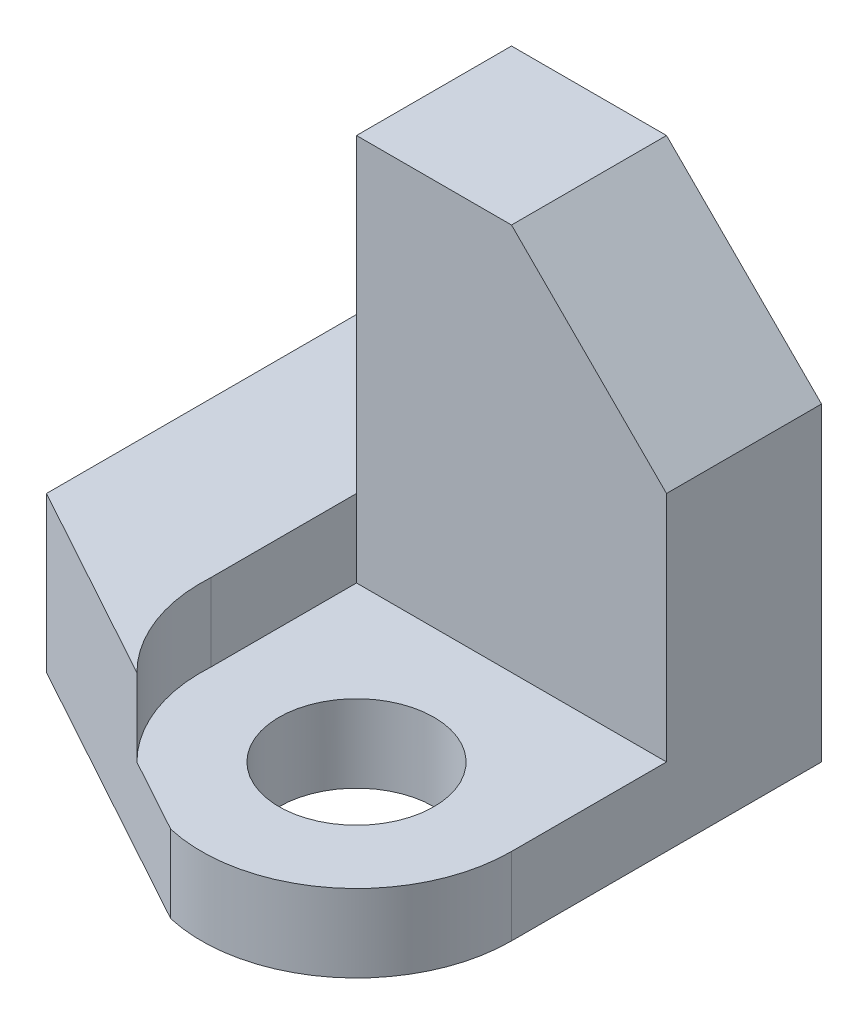
SolidWorks part; units mm, degrees
ref_plane "Front" through (0, 0, 0) normal (0, 0, 1) x (1, 0, 0)
ref_plane "Top" through (0, 0, 0) normal (0, 1, 0) x (1, 0, 0)
ref_plane "Right" through (0, 0, 0) normal (1, 0, 0) x (0, 0, -1)
sketch "Sketch1" plane through (0, 0, 0) normal (0, 1, 0) x (1, 0, 0)
  line L0 (0, 0) -> (4, 0)
  line L1 (4, 0) -> (4, -4)
  line L2 (0, -4) -> (0, 0)
  line L3 (0, 0) -> (-2, 0)
  line L4 (-2, 0) -> (-2, -4)
  line L5 (-2, -4) -> (1.5528, -5.9494)
  arc A0 (4, -4) -> (0, -4) centre (2, -4) cw
  circle A1 centre (2, -4) radius 1
  dimension "D5" = 2
  dimension "D1" = 4
  dimension "D2" = 4
  dimension "D3" = 2
  dimension "D4" = 4
extrude "Boss-Extrude1" add sketch "Sketch1" along normal blind 2 contours L5 A0 L2 L3 L4 | A0 L5 L1 L0 L2 A1
sketch "Sketch2" plane through (0, 2, 0) normal (0, 1, 0) x (1, 0, 0)
  line L0 (0, 0) -> (4, 0)
  line L1 (4, 0) -> (4, -4)
  line L2 (0, -3.8752) -> (0, 0)
  arc A0 (1.5528, -5.9494) -> (4, -4) centre (2, -4) ccw construction
  arc A1 (4, -4) -> (0, -3.8752) centre (1.9981, -4) cw
extrude "Cut-Extrude1" cut sketch "Sketch2" against normal blind 1
sketch "Sketch3" plane through (0, 1, 0) normal (0, 1, 0) x (1, 0, 0)
  line L0 (4, -4) -> (4, 0) construction
  line L1 (0, 0) -> (4, 0)
  line L2 (0, 0) -> (0, -2)
  line L3 (0, -2) -> (4, -2)
  line L4 (4, 0) -> (4, -2)
  dimension "D1" = 2
extrude "Boss-Extrude2" add sketch "Sketch3" along normal blind 5
chamfer "Chamfer1" distance 2 angle 45 1 edges at (4, 6, 1)
